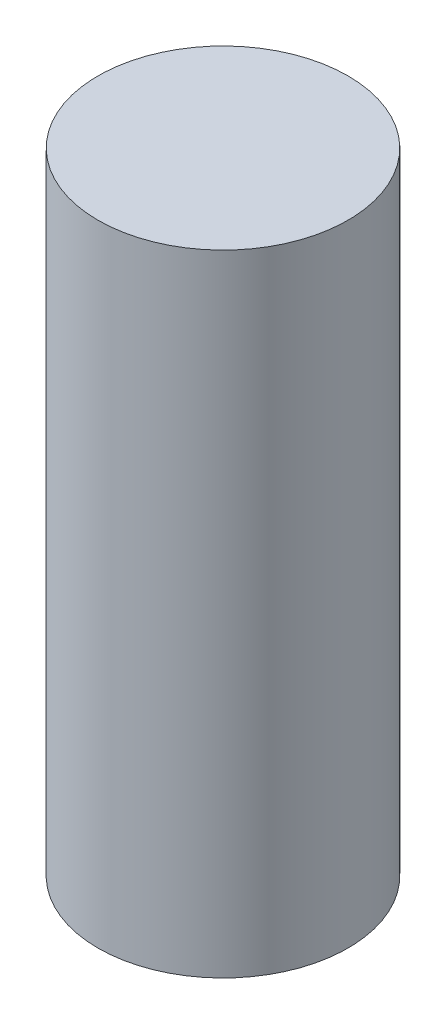
SolidWorks part; units mm, degrees
ref_plane "Front" through (0, 0, 0) normal (0, 0, 1) x (1, 0, 0)
ref_plane "Top" through (0, 0, 0) normal (0, 1, 0) x (1, 0, 0)
ref_plane "Right" through (0, 0, 0) normal (1, 0, 0) x (0, 0, -1)
sketch "Sketch2" plane through (0, 0, 0) normal (0, 1, 0) x (1, 0, 0)
  circle A0 centre (0, 0) radius 18.034
  dimension "D1" = 36.068
extrude "Boss-Extrude1" add sketch "Sketch2" along normal blind 90.932
